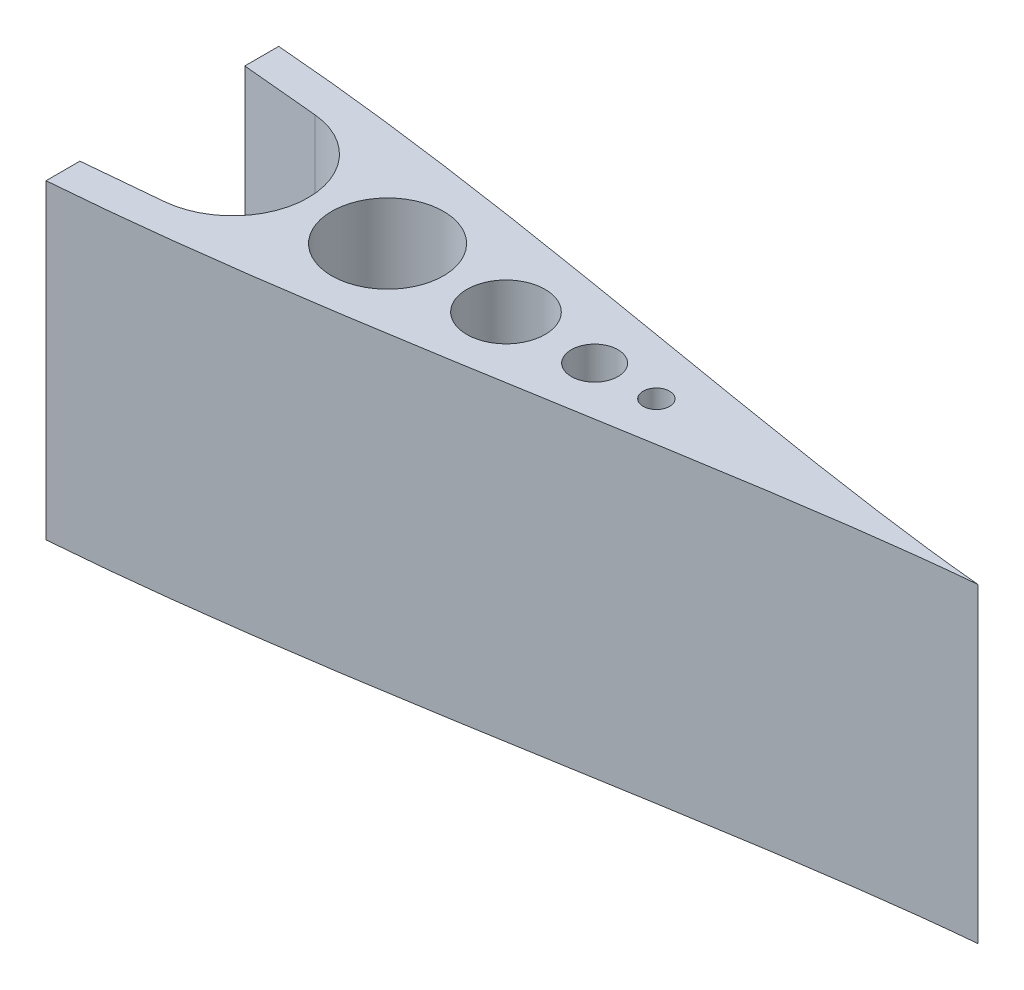
SolidWorks part; units mm, degrees
material "Polyurethane Foam Rigid"
ref_plane "Front Plane" through (0, 0, 0) normal (0, 0, 1) x (1, 0, 0)
ref_plane "Top Plane" through (0, 0, 0) normal (0, 1, 0) x (1, 0, 0)
ref_plane "Right Plane" through (0, 0, 0) normal (1, 0, 0) x (0, 0, -1)
sketch "Sketch1" plane through (0, 0, 0) normal (0, 1, 0) x (1, 0, 0)
  line L16 (-97.1704, 0) -> (-106.483, 0)
  line L17 (-45.5408, 15.24) -> (-13.8473, 12.2851)
  line L19 (-117.269, 0) -> (117.269, 0) construction
  line L20 (-45.5408, -15.24) -> (-13.8473, -12.2851)
  circle A1 centre (54.2104, 0) radius 2.159
  circle A2 centre (44.1263, 0) radius 3.81
  circle A3 centre (29.6435, 0) radius 6.3923
  circle A4 centre (10.3102, 0) radius 9.131
  arc A5 (-13.8473, -12.2851) -> (-13.8473, 12.2851) centre (-14.9927, 0) ccw
  arc A6 (-42.7236, 14.9773) -> (-42.7236, -14.9773) centre (-45.5408, 0) ccw
  circle A7 centre (-71.7704, 0) radius 5.715
  circle A8 centre (-92.9371, 0) radius 4.2333
  spline S0 degree 3 poles (-106.483, 0) (-106.482, -0.3362) (-106.4279, -1.1725) (-106.106, -2.6431) (-105.314, -4.4752) (-103.8975, -6.5043) (-101.808, -8.5717) (-99.0667, -10.5676) (-95.7198, -12.4267) (-91.8173, -14.1114) (-87.4067, -15.5993) (-82.5319, -16.8771) (-77.2341, -17.9374) (-71.5526, -18.7767) (-65.5251, -19.3955) (-59.1886, -19.7966) (-52.5791, -19.9863) (-45.732, -19.9729) (-38.6824, -19.7673) (-31.4645, -19.3826) (-24.1123, -18.8333) (-16.6591, -18.136) (-9.1376, -17.3083) (-1.5801, -16.3689) (5.9818, -15.3372) (13.5169, -14.233) (20.9946, -13.0761) (28.385, -11.8862) (35.6583, -10.6823) (42.7857, -9.4828) (49.7386, -8.3046) (56.4893, -7.1638) (63.0103, -6.0744) (69.2751, -5.0488) (75.2578, -4.0977) (80.9333, -3.2293) (86.2777, -2.4498) (91.2676, -1.7633) (95.8816, -1.1712) (100.0981, -0.6731) (103.6732, -0.2905) (105.8361, -0.0817) (106.7334, 0) knots 0.5 0.5 0.5 0.5 0.502167 0.50539 0.509656 0.514948 0.521245 0.528521 0.536745 0.545881 0.555891 0.56673 0.578353 0.59071 0.603747 0.61741 0.631639 0.646374 0.661552 0.677107 0.692975 0.709086 0.725371 0.741762 0.758188 0.774579 0.790865 0.806976 0.822844 0.8384 0.853578 0.868314 0.882544 0.896207 0.909245 0.921603 0.933227 0.944068 0.95408 0.963219 0.971447 0.977251 0.977251 0.977251 0.977251
  spline S1 degree 3 poles (-106.483, 0) (-106.482, 0.3362) (-106.4279, 1.1725) (-106.106, 2.6431) (-105.314, 4.4752) (-103.8975, 6.5043) (-101.808, 8.5717) (-99.0667, 10.5676) (-95.7198, 12.4267) (-91.8173, 14.1114) (-87.4067, 15.5993) (-82.5319, 16.8771) (-77.2341, 17.9374) (-71.5526, 18.7767) (-65.5251, 19.3955) (-59.1886, 19.7966) (-52.5791, 19.9863) (-45.732, 19.9729) (-38.6824, 19.7673) (-31.4645, 19.3826) (-24.1123, 18.8333) (-16.6591, 18.136) (-9.1376, 17.3083) (-1.5801, 16.3689) (5.9818, 15.3372) (13.5169, 14.233) (20.9946, 13.0761) (28.385, 11.8862) (35.6583, 10.6823) (42.7857, 9.4828) (49.7386, 8.3046) (56.4893, 7.1638) (63.0103, 6.0744) (69.2751, 5.0488) (75.2578, 4.0977) (80.9333, 3.2293) (86.2777, 2.4498) (91.2676, 1.7633) (95.8816, 1.1712) (100.0981, 0.6731) (103.6732, 0.2905) (105.8361, 0.0817) (106.7334, 0) knots 0.5 0.5 0.5 0.5 0.502167 0.50539 0.509656 0.514948 0.521245 0.528521 0.536745 0.545881 0.555891 0.56673 0.578353 0.59071 0.603747 0.61741 0.631639 0.646374 0.661552 0.677107 0.692975 0.709086 0.725371 0.741762 0.758188 0.774579 0.790865 0.806976 0.822844 0.8384 0.853578 0.868314 0.882544 0.896207 0.909245 0.921603 0.933227 0.944068 0.95408 0.963219 0.971447 0.977251 0.977251 0.977251 0.977251
  dimension "D1" = 11.43
  dimension "D2" = 30.48
  dimension "D3" = 26.2296
extrude "Boss-Extrude1" add sketch "Sketch1" along normal blind 50.8
sketch "Sketch2" plane through (0, 50.8, 0) normal (0, 1, 0) x (1, 0, 0)
  line L0 (-26.473, 19.0015) -> (-26.473, -19.0015)
  spline S0 degree 3 poles (1101.7973, -2735.4284) (115.4736, 98.2897) (-114.0593, 33.6853) (-106.106, -2.6431) (-105.314, -4.4752) (-103.8975, -6.5043) (-101.808, -8.5717) (-99.0667, -10.5676) (-95.7198, -12.4267) (-91.8173, -14.1114) (-87.4067, -15.5993) (-82.5319, -16.8771) (-77.2341, -17.9374) (-71.5526, -18.7767) (-65.5251, -19.3955) (-59.1886, -19.7966) (-52.5791, -19.9863) (-45.732, -19.9729) (-38.6824, -19.7673) (-31.4645, -19.3826) (-24.1123, -18.8333) (-16.6591, -18.136) (-9.1376, -17.3083) (-1.5801, -16.3689) (5.9818, -15.3372) (13.5169, -14.233) (20.9946, -13.0761) (28.385, -11.8862) (35.6583, -10.6823) (42.7857, -9.4828) (49.7386, -8.3046) (56.4893, -7.1638) (63.0103, -6.0744) (69.2751, -5.0488) (75.2578, -4.0977) (80.9333, -3.2293) (86.2777, -2.4498) (91.2676, -1.7633) (95.8816, -1.1712) (100.0981, -0.6731) (189.3, 8.8732) (273.7921, -19.424) (3023.8105, -699.248) knots 0.271128 0.271128 0.271128 0.271128 0.502167 0.50539 0.509656 0.514948 0.521245 0.528521 0.536745 0.545881 0.555891 0.56673 0.578353 0.59071 0.603747 0.61741 0.631639 0.646374 0.661552 0.677107 0.692975 0.709086 0.725371 0.741762 0.758188 0.774579 0.790865 0.806976 0.822844 0.8384 0.853578 0.868314 0.882544 0.896207 0.909245 0.921603 0.933227 0.944068 0.95408 0.963219 0.971447 1.532224 1.532224 1.532224 1.532224 only from (-106.483, 0) to (106.7334, 0) construction
  spline S1 degree 3 poles (1101.7973, 2735.4284) (115.4736, -98.2897) (-114.0593, -33.6853) (-106.106, 2.6431) (-105.314, 4.4752) (-103.8975, 6.5043) (-101.808, 8.5717) (-99.0667, 10.5676) (-95.7198, 12.4267) (-91.8173, 14.1114) (-87.4067, 15.5993) (-82.5319, 16.8771) (-77.2341, 17.9374) (-71.5526, 18.7767) (-65.5251, 19.3955) (-59.1886, 19.7966) (-52.5791, 19.9863) (-45.732, 19.9729) (-38.6824, 19.7673) (-31.4645, 19.3826) (-24.1123, 18.8333) (-16.6591, 18.136) (-9.1376, 17.3083) (-1.5801, 16.3689) (5.9818, 15.3372) (13.5169, 14.233) (20.9946, 13.0761) (28.385, 11.8862) (35.6583, 10.6823) (42.7857, 9.4828) (49.7386, 8.3046) (56.4893, 7.1638) (63.0103, 6.0744) (69.2751, 5.0488) (75.2578, 4.0977) (80.9333, 3.2293) (86.2777, 2.4498) (91.2676, 1.7633) (95.8816, 1.1712) (100.0981, 0.6731) (189.3, -8.8732) (273.7921, 19.424) (3023.8105, 699.248) knots 0.271128 0.271128 0.271128 0.271128 0.502167 0.50539 0.509656 0.514948 0.521245 0.528521 0.536745 0.545881 0.555891 0.56673 0.578353 0.59071 0.603747 0.61741 0.631639 0.646374 0.661552 0.677107 0.692975 0.709086 0.725371 0.741762 0.758188 0.774579 0.790865 0.806976 0.822844 0.8384 0.853578 0.868314 0.882544 0.896207 0.909245 0.921603 0.933227 0.944068 0.95408 0.963219 0.971447 1.532224 1.532224 1.532224 1.532224 only from (-106.483, 0) to (106.7334, 0) construction
  spline S2 degree 3 poles (-106.483, 0) (-106.482, -0.3362) (-106.4279, -1.1725) (-106.106, -2.6431) (-105.314, -4.4752) (-103.8975, -6.5043) (-101.808, -8.5717) (-99.0667, -10.5676) (-95.7198, -12.4267) (-91.8173, -14.1114) (-87.4067, -15.5993) (-82.5319, -16.8771) (-77.2341, -17.9374) (-71.5526, -18.7767) (-65.5251, -19.3955) (-59.1886, -19.7966) (-52.5791, -19.9863) (-45.732, -19.9729) (-38.6824, -19.7673) (-32.2397, -19.4239) (-28.1526, -19.1325) (-26.473, -19.0015) knots 0.5 0.5 0.5 0.5 0.502167 0.50539 0.509656 0.514948 0.521245 0.528521 0.536745 0.545881 0.555891 0.56673 0.578353 0.59071 0.603747 0.61741 0.631639 0.646374 0.661552 0.677107 0.68797 0.68797 0.68797 0.68797
  spline S3 degree 3 poles (-106.483, 0) (-106.482, 0.3362) (-106.4279, 1.1725) (-106.106, 2.6431) (-105.314, 4.4752) (-103.8975, 6.5043) (-101.808, 8.5717) (-99.0667, 10.5676) (-95.7198, 12.4267) (-91.8173, 14.1114) (-87.4067, 15.5993) (-82.5319, 16.8771) (-77.2341, 17.9374) (-71.5526, 18.7767) (-65.5251, 19.3955) (-59.1886, 19.7966) (-52.5791, 19.9863) (-45.732, 19.9729) (-38.6824, 19.7673) (-32.2397, 19.4239) (-28.1526, 19.1325) (-26.473, 19.0015) knots 0.5 0.5 0.5 0.5 0.502167 0.50539 0.509656 0.514948 0.521245 0.528521 0.536745 0.545881 0.555891 0.56673 0.578353 0.59071 0.603747 0.61741 0.631639 0.646374 0.661552 0.677107 0.68797 0.68797 0.68797 0.68797
  dimension "D1" = 80.01
extrude "Cut-Extrude1" cut sketch "Sketch2" against normal through all
